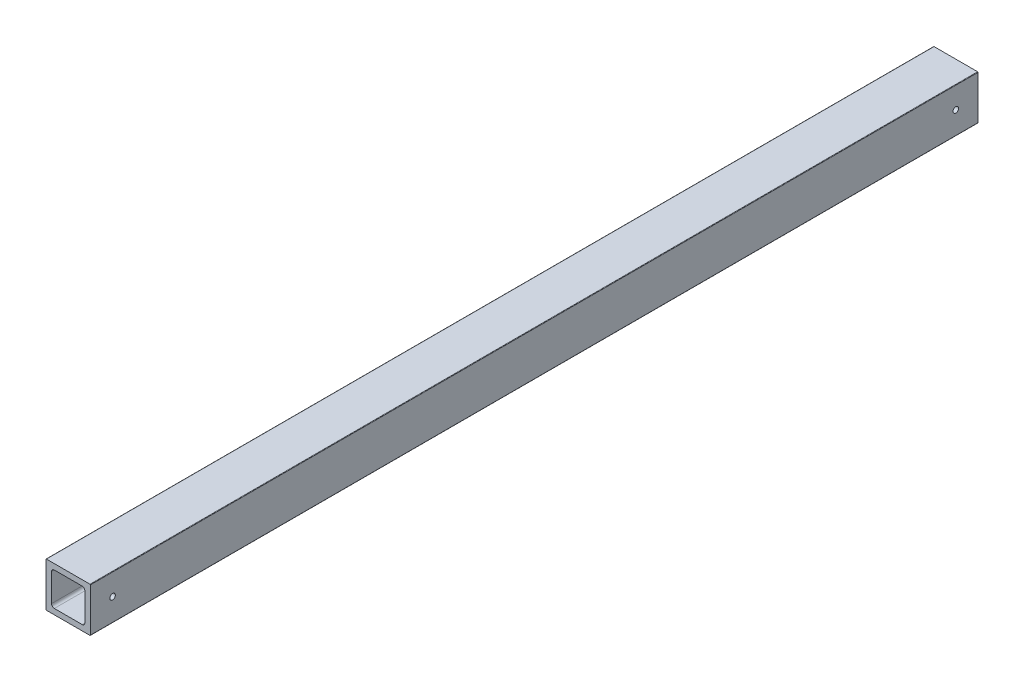
SolidWorks part; units mm, degrees
ref_plane "Front Plane" through (0, 0, 0) normal (0, 0, 1) x (1, 0, 0)
ref_plane "Top Plane" through (0, 0, 0) normal (0, 1, 0) x (1, 0, 0)
ref_plane "Right Plane" through (0, 0, 0) normal (1, 0, 0) x (0, 0, -1)
ref_plane "Plane1" through (0, 0, 0) normal (0, 0, -1) x (-1, 0, 0)
sketch "Sketch1" plane through (0, 0, 0) normal (0, 0, -1) x (-1, 0, 0)
  line L0 (-3.175, 20.6375) -> (-3.175, 4.7625)
  line L1 (-4.7625, 3.175) -> (-20.6375, 3.175)
  line L2 (-22.225, 4.7625) -> (-22.225, 20.6375)
  line L3 (-20.6375, 22.225) -> (-4.7625, 22.225)
  line L4 (0, 0.254) -> (0, 25.146)
  line L5 (-0.254, 25.4) -> (-25.146, 25.4)
  line L6 (-25.4, 25.146) -> (-25.4, 0.254)
  line L7 (-25.146, 0) -> (-0.254, 0)
  arc A0 (-3.175, 4.7625) -> (-4.7625, 3.175) centre (-4.7625, 4.7625) cw
  arc A1 (-20.6375, 3.175) -> (-22.225, 4.7625) centre (-20.6375, 4.7625) cw
  arc A2 (-22.225, 20.6375) -> (-20.6375, 22.225) centre (-20.6375, 20.6375) cw
  arc A3 (-4.7625, 22.225) -> (-3.175, 20.6375) centre (-4.7625, 20.6375) cw
  arc A4 (-0.254, 0) -> (0, 0.254) centre (-0.254, 0.254) ccw
  arc A5 (0, 25.146) -> (-0.254, 25.4) centre (-0.254, 25.146) ccw
  arc A6 (-25.146, 25.4) -> (-25.4, 25.146) centre (-25.146, 25.146) ccw
  arc A7 (-25.4, 0.254) -> (-25.146, 0) centre (-25.146, 0.254) ccw
  dimension "D1" = 25.4
  dimension "D2" = 25.4
  dimension "D3" = 19.05
  dimension "D4" = 3.175
  dimension "D5" = 19.05
extrude "Boss-Extrude1" add sketch "Sketch1" against normal blind 508
sketch "Sketch2" plane through (0, 0, 0) normal (-1, 0, 0) x (0, 0, 1)
  line L0 (0, 0.254) -> (0, 25.146) construction
  line L1 (508, 0.254) -> (0, 0.254) construction
  line L2 (508, 0.254) -> (508, 25.146) construction
  circle A0 centre (12.6975, 12.954) radius 1.5875
  circle A1 centre (495.3, 12.954) radius 1.5875
  point P4 (0, 12.7)
  dimension "D1" = 3.175
  dimension "D2" = 12.7
  dimension "D3" = 12.7
  dimension "D4" = 3.175
  dimension "D5" = 12.7
  dimension "D6" = 12.7
extrude "Cut-Extrude1" cut sketch "Sketch2" against normal through all
